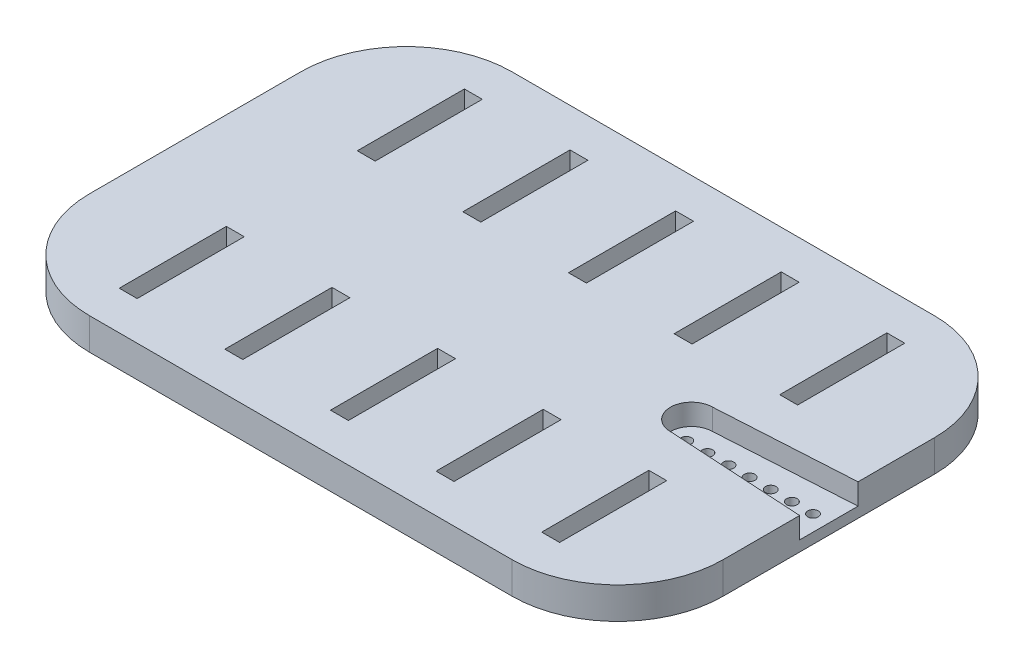
SolidWorks part; units mm, degrees
ref_plane "前视基准面" through (0, 0, 0) normal (0, 0, 1) x (1, 0, 0)
ref_plane "上视基准面" through (0, 0, 0) normal (0, 1, 0) x (1, 0, 0)
ref_plane "右视基准面" through (0, 0, 0) normal (1, 0, 0) x (0, 0, -1)
sketch "草图1" plane through (0, 0, 0) normal (0, 1, 0) x (1, 0, 0)
  line L1 (-30, 20) -> (30, 20)
  line L2 (-30, 20) -> (-30, -20)
  line L3 (-30, -20) -> (30, -20)
  line L4 (30, 20) -> (30, -20)
  line L5 (-30, 20) -> (30, -20) construction
  line L6 (-30, -20) -> (30, 20) construction
  point P0 (0, 0)
  dimension "D1" = 60
  dimension "D2" = 40
extrude "凸台-拉伸1" add sketch "草图1" along normal blind 3
fillet "圆角1" radius 10 4 edges at (-30, 1.5, 20) (30, 1.5, 20) (30, 1.5, -20) (-30, 1.5, -20)
sketch "草图2" plane through (0, 3, 0) normal (0, 1, 0) x (1, 0, 0)
  line L0 (-30, 0) -> (30, 0) construction
  line L1 (-30, 10) -> (-30, -10) construction
  line L2 (30, -10) -> (30, 10) construction
  line L3 (0, 20) -> (0, -20) construction
  line L4 (20, 20) -> (-20, 20) construction
  line L5 (-20, -20) -> (20, -20) construction
  line L6 (-20, 0) -> (40, 0) construction
  line L7 (-20.848, 16.3403) -> (-19.152, 16.3403)
  line L8 (-20.848, 16.3403) -> (-20.848, 6.198)
  line L9 (-20.848, 6.198) -> (-19.152, 6.198)
  line L10 (-19.152, 16.3403) -> (-19.152, 6.198)
  line L11 (-20.848, 16.3403) -> (-19.152, 6.198) construction
  line L12 (-20.848, 6.198) -> (-19.152, 16.3403) construction
  line L13 (-9.152, 16.3403) -> (-9.152, 6.198)
  line L14 (-10.848, 16.3403) -> (-9.152, 16.3403)
  line L15 (-10.848, 16.3403) -> (-10.848, 6.198)
  line L16 (-10.848, 6.198) -> (-9.152, 6.198)
  line L17 (-10, 0) -> (50, 0) construction
  line L18 (0.848, 16.3403) -> (0.848, 6.198)
  line L19 (-0.848, 16.3403) -> (0.848, 16.3403)
  line L20 (-0.848, 16.3403) -> (-0.848, 6.198)
  line L21 (-0.848, 6.198) -> (0.848, 6.198)
  line L22 (0, 0) -> (60, 0) construction
  line L23 (10.848, 16.3403) -> (10.848, 6.198)
  line L24 (9.152, 16.3403) -> (10.848, 16.3403)
  line L25 (9.152, 16.3403) -> (9.152, 6.198)
  line L26 (9.152, 6.198) -> (10.848, 6.198)
  line L27 (10, 0) -> (70, 0) construction
  line L28 (20.848, 16.3403) -> (20.848, 6.198)
  line L29 (19.152, 16.3403) -> (20.848, 16.3403)
  line L30 (19.152, 16.3403) -> (19.152, 6.198)
  line L31 (19.152, 6.198) -> (20.848, 6.198)
  line L32 (19.152, -6.198) -> (20.848, -6.198)
  line L33 (20.848, -16.3403) -> (20.848, -6.198)
  line L34 (19.152, -16.3403) -> (20.848, -16.3403)
  line L35 (19.152, -16.3403) -> (19.152, -6.198)
  line L36 (9.152, -6.198) -> (10.848, -6.198)
  line L37 (10.848, -16.3403) -> (10.848, -6.198)
  line L38 (9.152, -16.3403) -> (10.848, -16.3403)
  line L39 (9.152, -16.3403) -> (9.152, -6.198)
  line L40 (-0.848, -6.198) -> (0.848, -6.198)
  line L41 (0.848, -16.3403) -> (0.848, -6.198)
  line L42 (-0.848, -16.3403) -> (0.848, -16.3403)
  line L43 (-0.848, -16.3403) -> (-0.848, -6.198)
  line L44 (-10.848, -6.198) -> (-9.152, -6.198)
  line L45 (-9.152, -16.3403) -> (-9.152, -6.198)
  line L46 (-10.848, -16.3403) -> (-9.152, -16.3403)
  line L47 (-10.848, -16.3403) -> (-10.848, -6.198)
  line L48 (-20.848, -6.198) -> (-19.152, -6.198)
  line L49 (-19.152, -16.3403) -> (-19.152, -6.198)
  line L50 (-20.848, -16.3403) -> (-19.152, -16.3403)
  line L51 (-20.848, -16.3403) -> (-20.848, -6.198)
  point P12 (-20, 11.2692)
  point P18 (0, 16.3403)
  dimension "D1" = 5
extrude "切除-拉伸1" cut sketch "草图2" against normal through all
sketch "草图3" plane through (0, 3, 0) normal (0, 1, 0) x (1, 0, 0)
  line L0 (30, 0) -> (-30, 0) construction
  line L1 (30, -10) -> (30, 10) construction
  line L2 (-30, 10) -> (-30, -10) construction
  line L5 (30, 5.6904) -> (30, 0) construction
  line L6 (30, 0) -> (30, -5.5802) construction
  line L7 (34, 3) -> (34, -3)
  line L8 (34, 0) -> (30, 0) construction
  line L10 (17, 2) -> (34, 3)
  line L11 (17, -2) -> (34, -3)
  arc A0 (17, 2) -> (17, -2) centre (17, 0) ccw
  point P12 (15, 0)
  dimension "D2" = 4
  dimension "D3" = 4
  dimension "D1" = 6
  dimension "D4" = 19
extrude "切除-拉伸2" cut sketch "草图3" against normal blind 2
sketch "草图4" plane through (0, 1, 0) normal (0, 1, 0) x (1, 0, 0)
  line L0 (15, 0) -> (30, 0) construction
  line L1 (30, -2.7647) -> (30, 2.7647) construction
  arc A0 (17, 2) -> (17, -2) centre (17, 0) ccw construction
  circle A1 centre (16.5, 0) radius 0.5
  circle A2 centre (18.5, 0) radius 0.5
  circle A3 centre (20.5, 0) radius 0.5
  circle A4 centre (22.5, 0) radius 0.5
  circle A5 centre (24.5, 0) radius 0.5
  circle A6 centre (26.5, 0) radius 0.5
  circle A7 centre (28.5, 0) radius 0.5
  dimension "D1" = 1
  dimension "D2" = 1.5
  dimension "D3" = 7
extrude "切除-拉伸3" cut sketch "草图4" against normal through all
